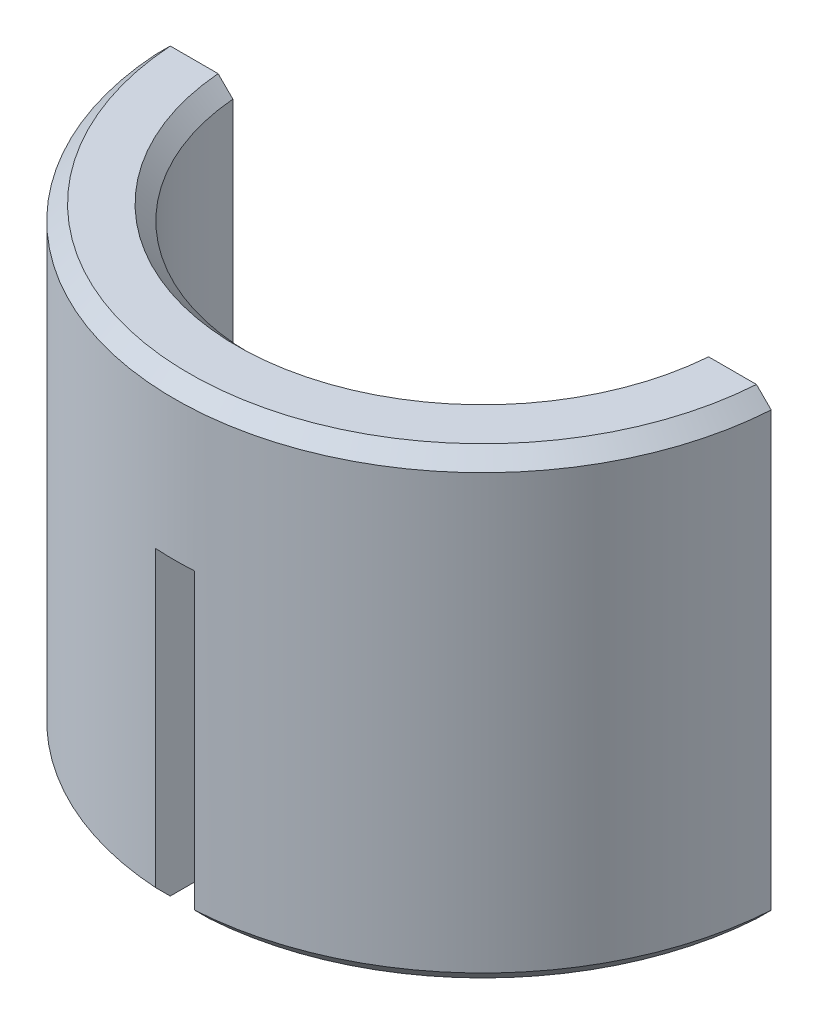
SolidWorks part; units mm, degrees
material "Alloy Steel"
ref_plane "Front Plane" through (0, 0, 0) normal (0, 0, 1) x (1, 0, 0)
ref_plane "Top Plane" through (0, 0, 0) normal (0, 1, 0) x (1, 0, 0)
ref_plane "Right Plane" through (0, 0, 0) normal (1, 0, 0) x (0, 0, -1)
sketch "Sketch1" plane through (0, 0, 0) normal (0, 0, 1) x (1, 0, 0)
  line L0 (0, 0) -> (56.5859, 0) construction
  line L1 (0, 0) -> (0, 109.073) construction
  line L2 (3.25, 0) -> (3.25, 2)
  line L3 (3.25, 2) -> (6, 2)
  line L4 (6, 2) -> (6, 12)
  line L5 (6, 12) -> (8, 12)
  line L9 (8, 0) -> (3.25, 0)
  line L10 (8, 12) -> (8, 0)
  dimension "D1" = 6.5
  dimension "D2" = 12
  dimension "D3" = 12
  dimension "D7" = 2
  dimension "D8" = 16
revolve "Revolve1" add sketch "Sketch1" angle 360 about L1
chamfer "Chamfer1" distance 1.35 angle 45 1 edges at (0, 2, -3.25)
fillet "Fillet1" radius 0.25 1 edges at (0, 2, -6)
chamfer "Chamfer2" distance 0.381 angle 45 3 edges at (0, 0, -8) (0, 12, -8) (0, 12, -6)
sketch "Sketch2" plane through (0, 0, 0) normal (0, 1, 0) x (1, 0, 0)
  line L0 (0, 0) -> (15.3335, 0) construction
  line L2 (8, 8) -> (-8, 8)
  line L3 (8, 8) -> (8, -0.508)
  line L4 (8, -0.508) -> (-8, -0.508)
  line L5 (-8, 8) -> (-8, -0.508)
  circle A0 centre (0, 0) radius 8 construction
  circle A1 centre (0, 0) radius 8 construction
  dimension "D1" = 0.508
extrude "Cut-Extrude1" cut sketch "Sketch2" along normal through all
sketch "Sketch3" plane through (0, 0, 0) normal (0, 1, 0) x (1, 0, 0)
  line L0 (0, 0) -> (0, -9.626) construction
  line L2 (-0.508, -8) -> (0.508, -8)
  line L3 (-0.508, -8) -> (-0.508, 0)
  line L4 (-0.508, 0) -> (0.508, 0)
  line L5 (0.508, -8) -> (0.508, 0)
  arc A0 (-7.9839, -0.508) -> (7.9839, -0.508) centre (0, 0) ccw construction
  point P7 (0, 0)
  dimension "D1" = 1.016
extrude "Cut-Extrude2" cut sketch "Sketch3" along normal blind 8
scale "Scale2" scale about origin uniform scaling yes scale factor 1.001
